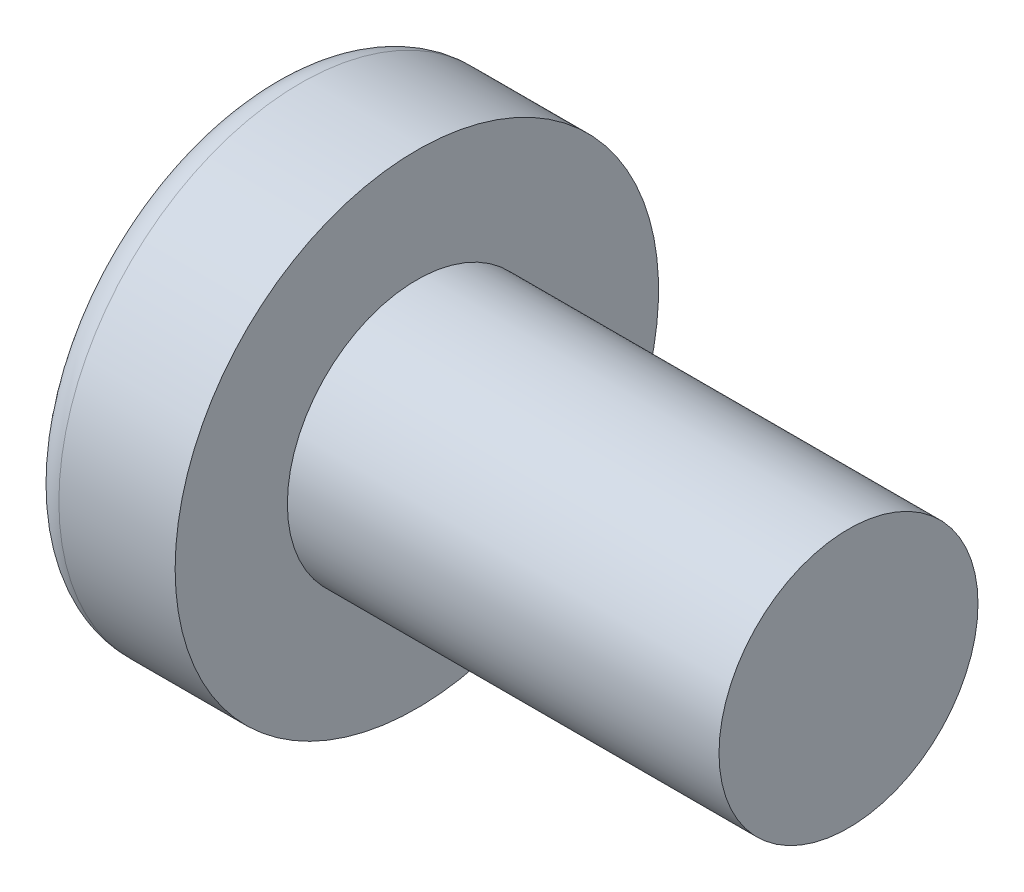
SolidWorks part; units mm, degrees
ref_plane "Plane1" through (0, 0, 0) normal (0, 0, 1) x (1, 0, 0)
ref_plane "Plane2" through (0, 0, 0) normal (0, 1, 0) x (1, 0, 0)
ref_plane "Plane3" through (0, 0, 0) normal (1, 0, 0) x (0, 0, -1)
sketch "BodySke" plane through (0, 0, 0) normal (0, 0, 1) x (1, 0, 0)
  line L0 (2.4, 1.5) -> (2.4, 2.8)
  line L1 (2.9, 6.35) -> (2.9, -3.175) construction
  line L2 (-25.4, 0) -> (127, 0) construction
  line L3 (7.4, 0) -> (0, 0)
  line L4 (2.4, 1.5) -> (7.4, 1.5)
  line L5 (7.4, 1.5) -> (7.4, 0)
  line L6 (1.0534, 2.8) -> (2.4, 2.8)
  line L7 (2.4, -1.5) -> (7.4, -1.5) construction
  line L8 (2.4, 6.35) -> (2.4, -3.175) construction
  arc A0 (0.7472, 2.6293) -> (0, 0) centre (5, 0) ccw
  arc A2 (0.7472, 2.6293) -> (1.0534, 2.8) centre (1.0534, 2.44) cw
  dimension "Head_crown_rad" = 5
  dimension "Head_fillet_rad" = 0.36
  dimension "Diameter" = 3
  dimension "Length" = 5
  dimension "Head_ht" = 2.4
  dimension "Head_dia" = 5.6
  dimension "Advance" = 0.5
  dimension "Thread_nom" = 5
revolve "Base-Revolve" add sketch "BodySke" angle 360 about L2
cosmetic thread "ThreadCosmetic" [suppressed] parameters "Thread_length"=4.5, "Thread_minor"=2.439
sketch "Sketch3" plane through (0, 0, 0) normal (1, 0, 0) x (0, 0, -1)
  line L0 (0.37, -1.45) -> (-0.37, -1.45)
  line L1 (0.37, -1.45) -> (0.37, 1.45)
  line L2 (-0.37, 1.45) -> (0.37, 1.45)
  line L3 (-0.37, 1.45) -> (-0.37, -1.45)
  dimension "Cross_dia" = 2.9
  dimension "D1" = 1.45
  dimension "Cross_width" = 0.74
  dimension "D2" = 0.37
ref_plane "Plane4" through (1.76, 0, 0) normal (1, 0, 0) x (0, 0, -1)
sketch "Sketch4" plane through (1.76, 0, 0) normal (1, 0, 0) x (0, 0, -1)
  line L0 (0.185, -0.185) -> (-0.185, -0.185)
  line L1 (0.185, -0.185) -> (0.185, 0.185)
  line L2 (-0.185, 0.185) -> (0.185, 0.185)
  line L3 (-0.185, 0.185) -> (-0.185, -0.185)
  dimension "D2" = 0.37
  dimension "D1" = 0.37
  dimension "D3" = 0.185
  dimension "D4" = 0.185
loft "Cut-Loft1" cut profiles "Sketch3", "Sketch4"
pattern_circular "CirPattern1" count 2 every 90 about axis through (0, 0, 0) along (1, 0, 0) of "Cut-Loft1"
sketch "ThdSchSke" plane through (0, 0, 0) normal (0, 0, 1) x (1, 0, 0)
  line L0 (2.9, -1.2195) -> (2.7036, -1.5)
  line L1 (2.9, -1.2195) -> (3.0964, -1.5)
  line L2 (3.0964, -1.5) -> (3.0964, -1.875)
  line L3 (-3.175, 0) -> (5.1513, 0) construction
  line L5 (3.0964, -1.875) -> (2.7036, -1.875)
  line L6 (2.7036, -1.875) -> (2.7036, -1.5)
  dimension "Diameter" = 3
  dimension "SideAngle" = 55
  dimension "VeeAngle" = 70
  dimension "Thread_minor" = 2.439
  dimension "Overcut" = 3.75
  dimension "Start" = 2.9
revolve "ThreadSchematic" [suppressed] cut sketch "ThdSchSke" angle 360 about L3
pattern_linear "ThdSchPat" [suppressed]
equation "\"D1@Sketch3\" = \"Cross_dia@Sketch3\" / 2"
equation "\"D2@Sketch3\" = \"Cross_width@Sketch3\" / 2"
equation "\"D1@Sketch4\" = \"Cross_width@Sketch3\" *.5"
equation "\"D2@Sketch4\" = \"D1@Sketch4\""
equation "\"D3@Sketch4\" = \"D1@Sketch4\" / 2"
equation "\"D4@Sketch4\" = \"D2@Sketch4\" / 2"
equation "\"Thread_length@ThreadCosmetic\" = ((sgn( (\"Length@BodySke\" - \"Advance@BodySke\" ) - \"Thread_nom@BodySke\" )-1)*( (\"Length@BodySke\" - \"Advance@BodySke\" ) - \"Thread_nom@BodySke\" ))/-2+ \"Thread_nom@BodySke\""
equation "\"Thread_minor@ThdSchSke\" = \"Thread_minor@ThreadCosmetic\""
equation "\"Diameter@ThdSchSke\" = \"Diameter@BodySke\""
equation "\"Overcut@ThdSchSke\" = \"Diameter@BodySke\" * 1.25"
equation "\"Start@ThdSchSke\" = \"Head_ht@BodySke\" + \"Length@BodySke\" - \"Thread_length@ThreadCosmetic\"  '---Non-countersunk---"
equation "\"Num_threads@ThdSchPat\" = int( \"Thread_length@ThreadCosmetic\" / \"Advance@BodySke\" + 0.999 )  + 1"
equation "\"Advance@ThdSchPat\" = \"Thread_length@ThreadCosmetic\" /  (\"Num_threads@ThdSchPat\" - 1) 'relax it"
